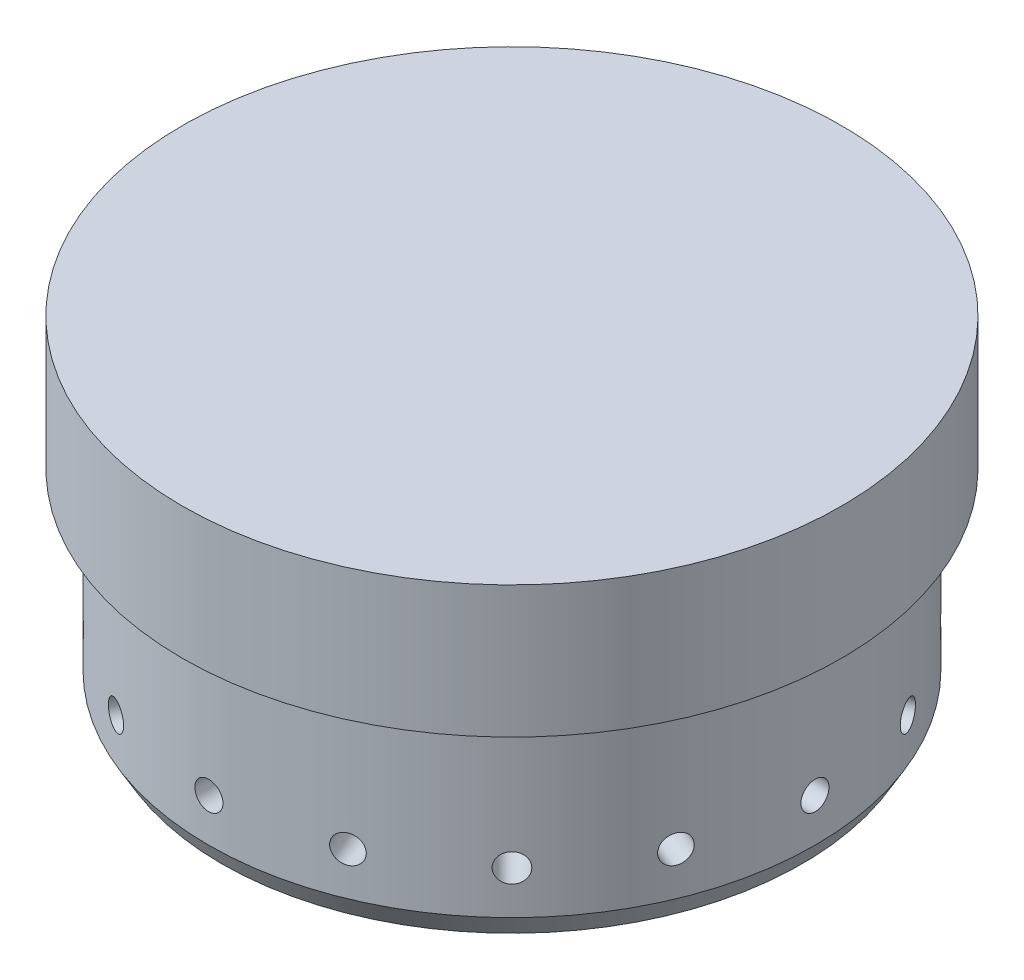
SolidWorks part; units mm, degrees
material "6061-T6 (SS)"
ref_plane "Front Plane" through (0, 0, 0) normal (0, 0, 1) x (1, 0, 0)
ref_plane "Top Plane" through (0, 0, 0) normal (0, 1, 0) x (1, 0, 0)
ref_plane "Right Plane" through (0, 0, 0) normal (1, 0, 0) x (0, 0, -1)
ref_axis "Center Axis" through (0, 0, 0) along (0, 1, 0)
sketch "Sketch1" plane through (0, 0, 0) normal (0, 0, 1) x (1, 0, 0)
  line L0 (0, 0) -> (-58.4454, 0)
  line L1 (-58.4454, 0) -> (-58.4454, 38.1)
  line L2 (-58.4454, 38.1) -> (-63.5, 38.1)
  line L3 (-63.5, 38.1) -> (-63.5, 63.5)
  line L4 (-63.5, 63.5) -> (0, 63.5)
  line L5 (0, 63.5) -> (0, 0)
revolve "Revolve1" add sketch "Sketch1" angle 360 about L5
ref_plane "Tap Reference Plane" through (0, 0, 58.4454) normal (0, 0, 1) x (1, 0, 0)
sketch "Hole Reference" plane through (0, 0, 58.4454) normal (0, 0, 1) x (1, 0, 0)
  line L0 (0, 0) -> (0, 12.7)
  point P4 (0, 12.7)
hole_wizard "1/4-28 Tap" positions "Sketch11" profile "Sketch13" hole size "1/4-28" standard "ANSI Inch"
sketch "Sketch11" plane through (0, 0, 58.4454) normal (0, 0, 1) x (1, 0, 0)
  point P0 (0, 12.7)
sketch "Sketch13" plane through (0, 12.7, 58.4454) normal (1, 0, 0) x (0, -1, 0)
  line L0 (0, 0) -> (0, 20.6754)
  line L1 (0, 20.6754) -> (2.7051, 19.05)
  line L2 (2.7051, 19.05) -> (2.7051, 0)
  line L5 (2.7051, 0) -> (0, 0)
  line L10 (0, 20.6754) -> (-2.7051, 19.05) construction
  line L11 (0, -6.35) -> (0, 107.95) construction
  dimension "Hole Dia." = 5.4102
  dimension "Hole Depth" = 19.05
  dimension "Drill Angle" = 118
pattern_circular "Tap Pattern" count 16 over 360 about axis through (0, 0, 0) along (0, 1, 0) of "1/4-28 Tap"
chamfer "Chamfer1" distance 2.54 angle 60 1 edges at (0, 0, 58.4454)
